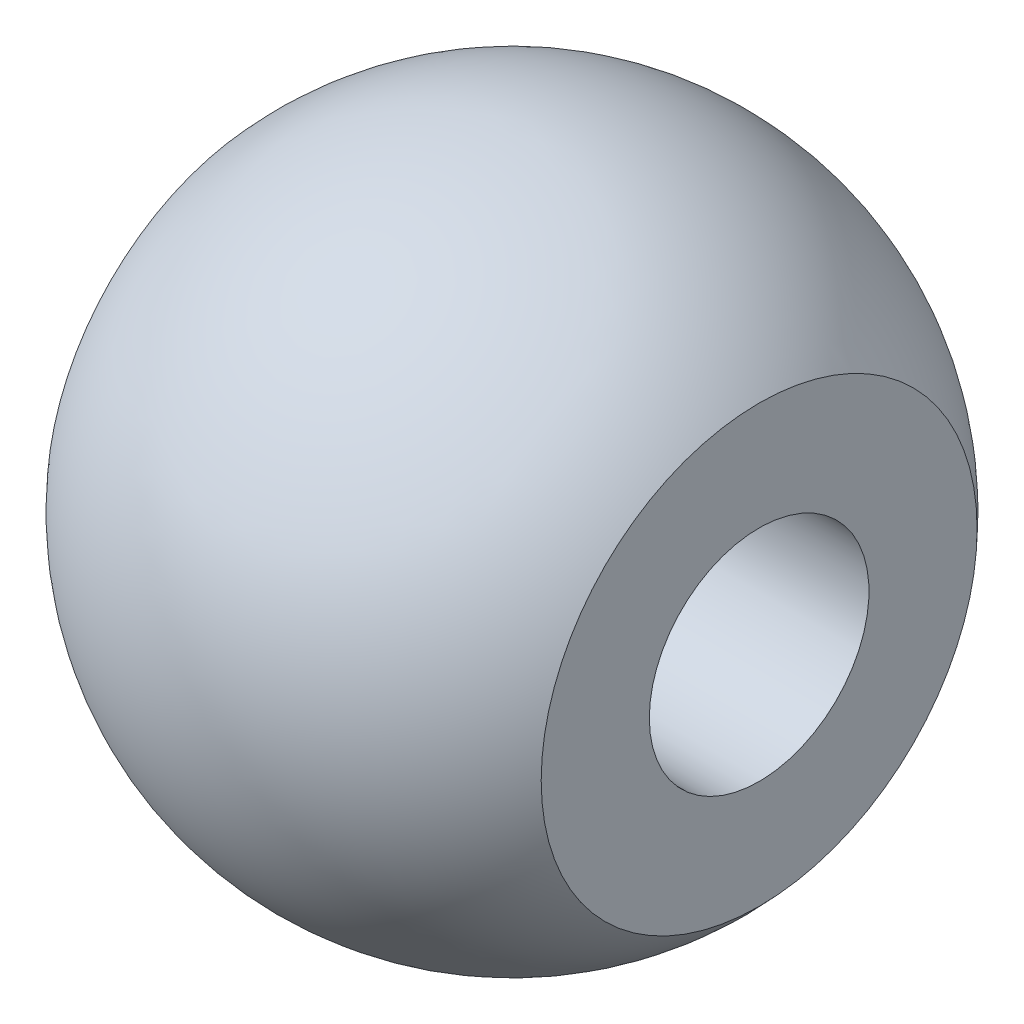
SolidWorks part; units mm, degrees
ref_plane "Front Plane" through (0, 0, 0) normal (0, 0, 1) x (1, 0, 0)
ref_plane "Top Plane" through (0, 0, 0) normal (0, 1, 0) x (1, 0, 0)
ref_plane "Right Plane" through (0, 0, 0) normal (1, 0, 0) x (0, 0, -1)
sketch "Sketch1" plane through (0, 0, 0) normal (0, 0, 1) x (1, 0, 0)
  line L0 (-4.5, 0) -> (4.5, 0)
  line L1 (4.5, -3.9686) -> (4.5, 0)
  line L2 (-4.5, -3.9686) -> (-4.5, 0)
  arc A1 (-4.5, -3.9686) -> (4.5, -3.9686) centre (0, 0) ccw
  point P6 (0, 0)
  point P9 (4.5, 0)
  point P12 (-4.5, 0)
  dimension "D1" = 6
  dimension "D2" = 9
  dimension "D3" = 4.5
revolve "Revolve1" add sketch "Sketch1" angle 360 about L0
sketch "Sketch2" plane through (0, 0, 0) normal (0, 1, 0) x (1, 0, 0)
  line L0 (-4.5, 0) -> (4.5, 0) construction
  line L1 (-4.5, 3.9686) -> (-4.5, -3.9686) construction
  line L2 (4.5, -3.9686) -> (4.5, 3.9686) construction
  line L3 (-4.5, 2) -> (4.5, 2) construction
  line L4 (-3.5, 2) -> (4.5, 2)
  line L5 (-4.5, 3) -> (-4.5, 0)
  line L6 (-4.5, 3) -> (-3.5, 2)
  line L7 (4.5, 2) -> (4.5, 0)
  line L8 (-4.5, 0) -> (4.5, 0)
  dimension "D2" = 2
revolve "Cut-Revolve1" cut sketch "Sketch2" angle 360 about L8
